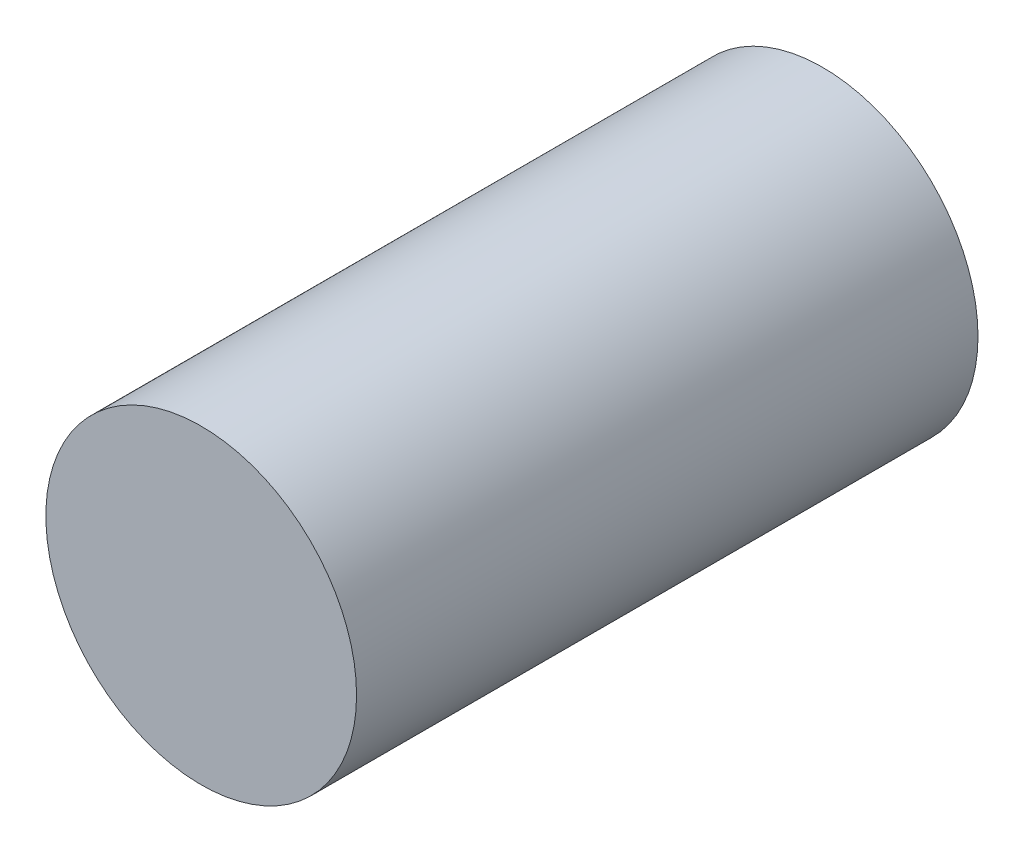
SolidWorks part; units mm, degrees
ref_plane "Front" through (0, 0, 0) normal (0, 0, 1) x (1, 0, 0)
ref_plane "Top" through (0, 0, 0) normal (0, 1, 0) x (1, 0, 0)
ref_plane "Right" through (0, 0, 0) normal (1, 0, 0) x (0, 0, -1)
sketch "Sketch1" plane through (0, 0, 0) normal (0, 0, 1) x (1, 0, 0)
  circle A0 centre (0, 0) radius 8.5
  dimension "D1" = 17
extrude "Boss-Extrude1" add sketch "Sketch1" along normal blind 34
